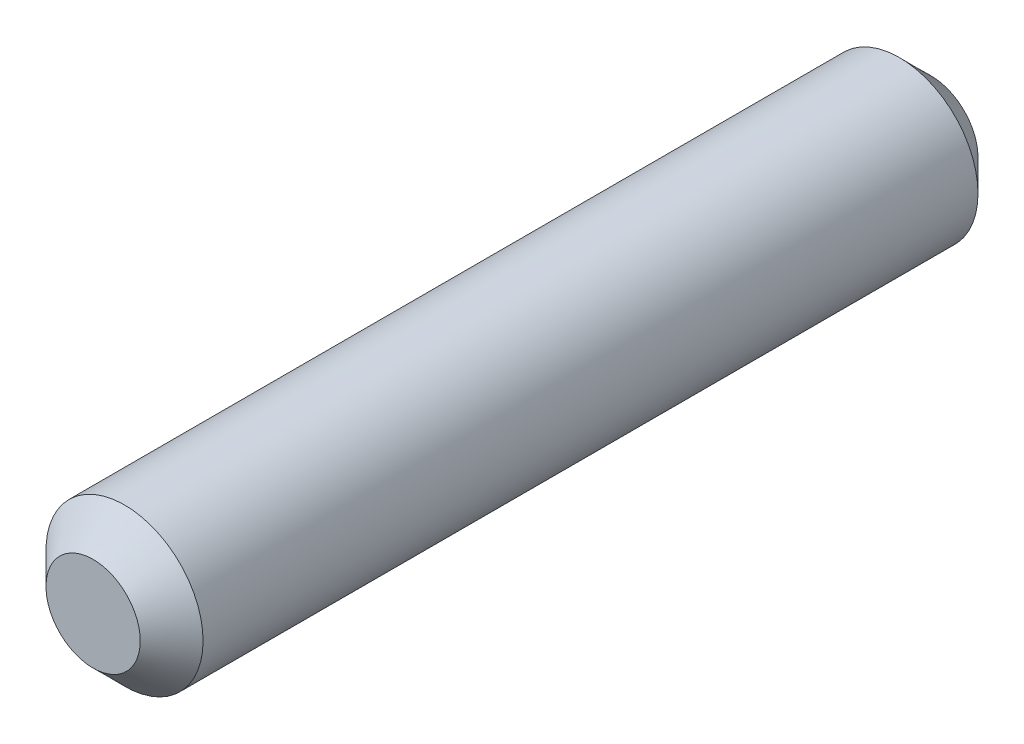
SolidWorks part; units mm, degrees
ref_plane "Front Plane" through (0, 0, 0) normal (0, 0, 1) x (1, 0, 0)
ref_plane "Top Plane" through (0, 0, 0) normal (0, 1, 0) x (1, 0, 0)
ref_plane "Right Plane" through (0, 0, 0) normal (1, 0, 0) x (0, 0, -1)
sketch "Sketch1" plane through (0, 0, 0) normal (0, 0, 1) x (1, 0, 0)
  circle A0 centre (0, 0) radius 1.5
extrude "Boss-Extrude1" add sketch "Sketch1" along normal blind 16
chamfer "Chamfer1" distance 0.6 angle 45 2 edges at (1.5, 0, 0) (1.5, 0, 16)
